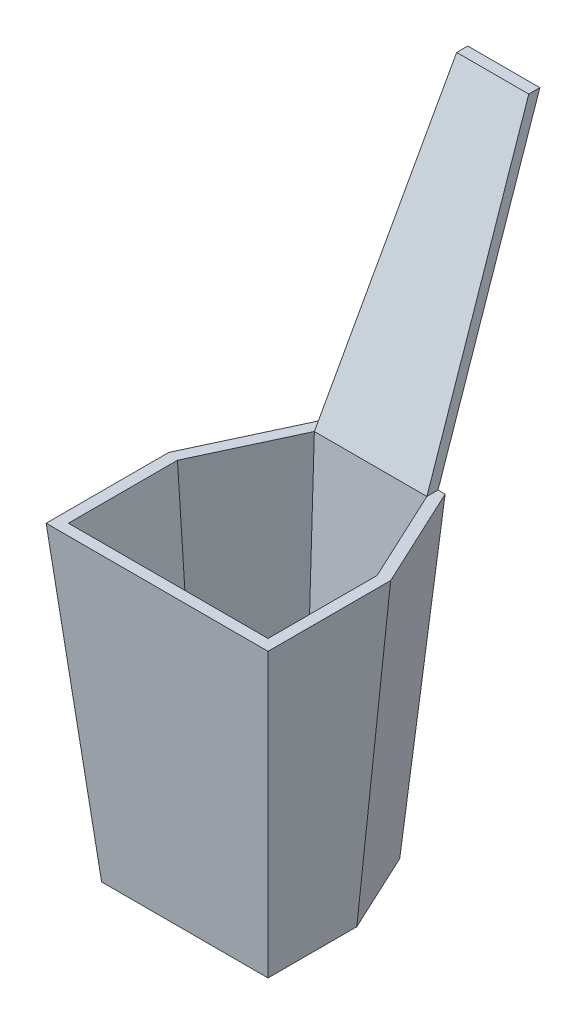
SolidWorks part; units mm, degrees
ref_plane "Front Plane" through (0, 0, 0) normal (0, 0, 1) x (1, 0, 0)
ref_plane "Top Plane" through (0, 0, 0) normal (0, 1, 0) x (1, 0, 0)
ref_plane "Right Plane" through (0, 0, 0) normal (1, 0, 0) x (0, 0, -1)
sketch "Sketch1" plane through (0, 0, 0) normal (0, 1, 0) x (1, 0, 0)
  line L0 (-10.4624, 28.5762) -> (10.4624, 28.5762)
  line L1 (10.4624, 28.5762) -> (19.05, 10.16)
  line L2 (19.05, 10.16) -> (19.05, -10.16)
  line L3 (19.05, -10.16) -> (-19.05, -10.16)
  line L4 (-19.05, -10.16) -> (-19.05, 10.16)
  line L5 (-19.05, 10.16) -> (-10.4624, 28.5762)
  dimension "D1" = 115
  dimension "D2" = 115
  dimension "D3" = 38.1
  dimension "D4" = 20.32
  dimension "D5" = 20.32
  dimension "D7" = 19.05
  dimension "D8" = 10.16
  dimension "D6" = 20.32
ref_plane "Plane1" through (0, 71.12, 0) normal (0, 1, 0) x (1, 0, 0)
sketch "Sketch3" plane through (0, 71.12, 0) normal (0, 1, 0) x (1, 0, 0)
  line L0 (-14.5078, 34.9262) -> (14.5078, 34.9262)
  line L1 (14.5078, 34.9262) -> (25.4, 11.5678)
  line L2 (25.4, 11.5678) -> (25.4, -16.51)
  line L3 (25.4, -16.51) -> (-25.4, -16.51)
  line L4 (-25.4, -16.51) -> (-25.4, 11.5678)
  line L6 (19.05, 10.16) -> (19.05, -10.16) construction
  line L7 (19.05, -10.16) -> (-19.05, -10.16) construction
  line L8 (-10.4624, 28.5762) -> (10.4624, 28.5762) construction
  line L9 (-19.05, -10.16) -> (-19.05, 10.16) construction
  line L10 (-14.5078, 34.9262) -> (-25.4, 11.5678)
  line L11 (10.4624, 28.5762) -> (19.05, 10.16) construction
  point P15 (0, 34.9262)
  point P16 (0, 28.5762)
  dimension "D1" = 6.35
  dimension "D2" = 6.35
  dimension "D3" = 6.35
  dimension "D4" = 6.35
  dimension "D5" = 0
  dimension "D6" = 115
  dimension "D7" = 115
  dimension "D8" = 6.35
loft "Loft2" add profiles "Sketch3", "Sketch1"
shell "Shell1" thickness 2.54
ref_plane "Plane2" through (0, 134.62, 0) normal (0, 1, 0) x (1, 0, 0)
sketch "Sketch6" plane through (0, 134.62, 0) normal (0, 1, 0) x (1, 0, 0)
  line L0 (-8.255, 62.8662) -> (8.255, 62.8662)
  line L3 (-8.255, 60.3262) -> (8.255, 60.3262)
  line L4 (14.5078, 34.9262) -> (-14.5078, 34.9262) construction
  line L5 (-8.255, 62.8662) -> (-8.255, 60.3262)
  line L6 (8.255, 60.3262) -> (8.255, 62.8662)
  point P2 (0, 60.3262)
  point P5 (0, 34.9262)
  dimension "D1" = 2.54
  dimension "D2" = 16.51
  dimension "D3" = 16.51
  dimension "D4" = 0
  dimension "D5" = 0
  dimension "D6" = 25.4
sketch "Sketch8" plane through (0, 71.12, 0) normal (0, 1, 0) x (1, 0, 0)
  line L0 (14.5078, 34.9262) -> (-14.5078, 34.9262) construction
  line L1 (-12.8832, 32.3761) -> (12.8832, 32.3761)
  line L2 (-12.8832, 32.3761) -> (-12.8832, 34.9262)
  line L3 (-12.8832, 34.9262) -> (12.8832, 34.9262)
  line L4 (12.8832, 32.3761) -> (12.8832, 34.9262)
  dimension "D1" = 0
loft "Loft3" add profiles "Sketch8", "Sketch6"
equation "\"D8@Sketch1\"=\"D4@Sketch1\"/2"
equation "\"D6@Sketch1\"=\"D5@Sketch1\""
equation "\"D7@Sketch1\"=\"D3@Sketch1\"/2"
